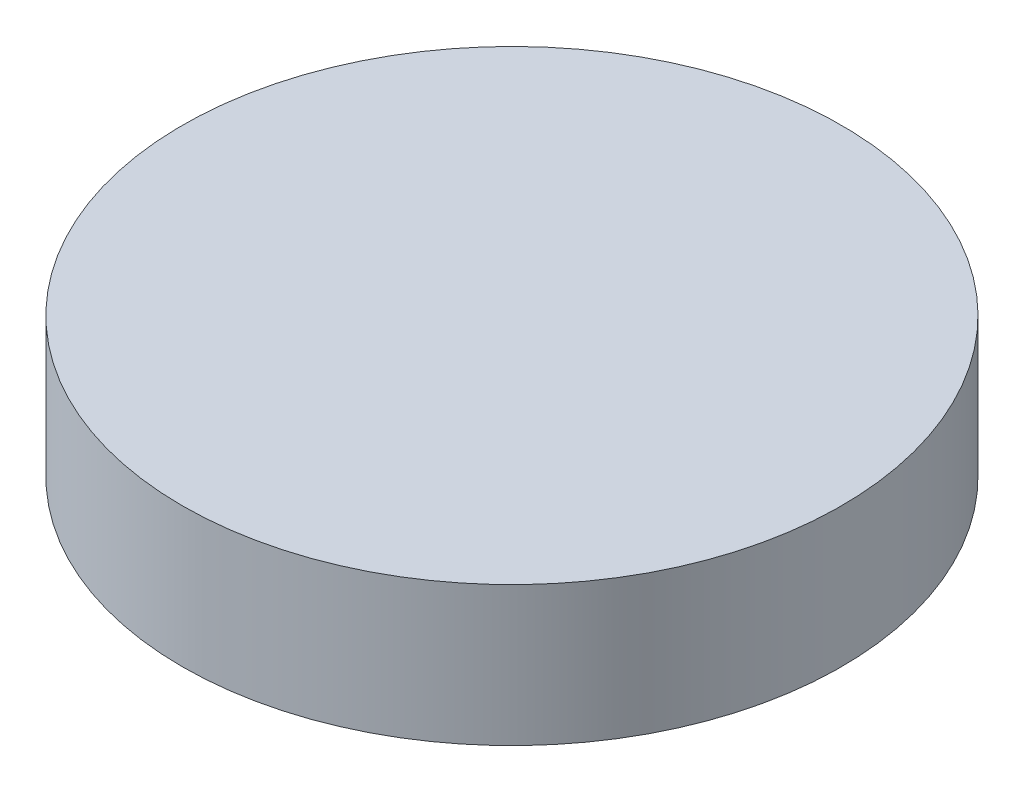
SolidWorks part; units mm, degrees
ref_plane "Front Plane" through (0, 0, 0) normal (0, 0, 1) x (1, 0, 0)
ref_plane "Top Plane" through (0, 0, 0) normal (0, 1, 0) x (1, 0, 0)
ref_plane "Right Plane" through (0, 0, 0) normal (1, 0, 0) x (0, 0, -1)
sketch "Sketch1" plane through (0, 0, 0) normal (0, 1, 0) x (1, 0, 0)
  circle A0 centre (0, 0) radius 36
  circle A1 centre (0, 0) radius 39
  dimension "D1" = 72
  dimension "D2" = 78
extrude "Boss-Extrude2" add sketch "Sketch1" along normal blind 8.5
sketch "Sketch2" plane through (0, 8.5, 0) normal (0, 1, 0) x (1, 0, 0)
  line L0 (0, 36) -> (0, -36) construction
  circle A0 centre (0, 0) radius 36 construction
  circle A1 centre (0, 0) radius 30
  circle A2 centre (0, 0) radius 39
  circle A3 centre (0, 0) radius 33 construction
  circle A4 centre (0, 33) radius 1.6986
  circle A5 centre (31.3849, 10.1976) radius 1.6986
  circle A6 centre (19.3969, -26.6976) radius 1.6986
  circle A7 centre (-19.3969, -26.6976) radius 1.6986
  circle A8 centre (-31.3849, 10.1976) radius 1.6986
  point P22 (0, 0)
  dimension "D1" = 60
  dimension "D2" = 78
  dimension "D3" = 66
  dimension "D4" = 3.3973
  dimension "D5" = 5
sketch "Sketch3" plane through (0, 0, 0) normal (0, 0, 1) x (1, 0, 0)
extrude "Boss-Extrude3" add sketch "Sketch2" along normal blind 3.2
sketch "Sketch4" plane through (0, 11.7, 0) normal (0, 1, 0) x (1, 0, 0)
  line L0 (0, -30) -> (0, 30) construction
  circle A0 centre (0, 0) radius 30 construction
  circle A1 centre (0, 0) radius 39
  circle A2 centre (0, 0) radius 30
  dimension "D1" = 78
  dimension "D2" = 60
extrude "Boss-Extrude6" add sketch "Sketch4" along normal blind 2.8
sketch "Sketch11" plane through (0, 14.5, 0) normal (0, 1, 0) x (1, 0, 0)
  circle A0 centre (0, 0) radius 39
  dimension "D1" = 78
extrude "Boss-Extrude7" add sketch "Sketch11" along normal blind 2
